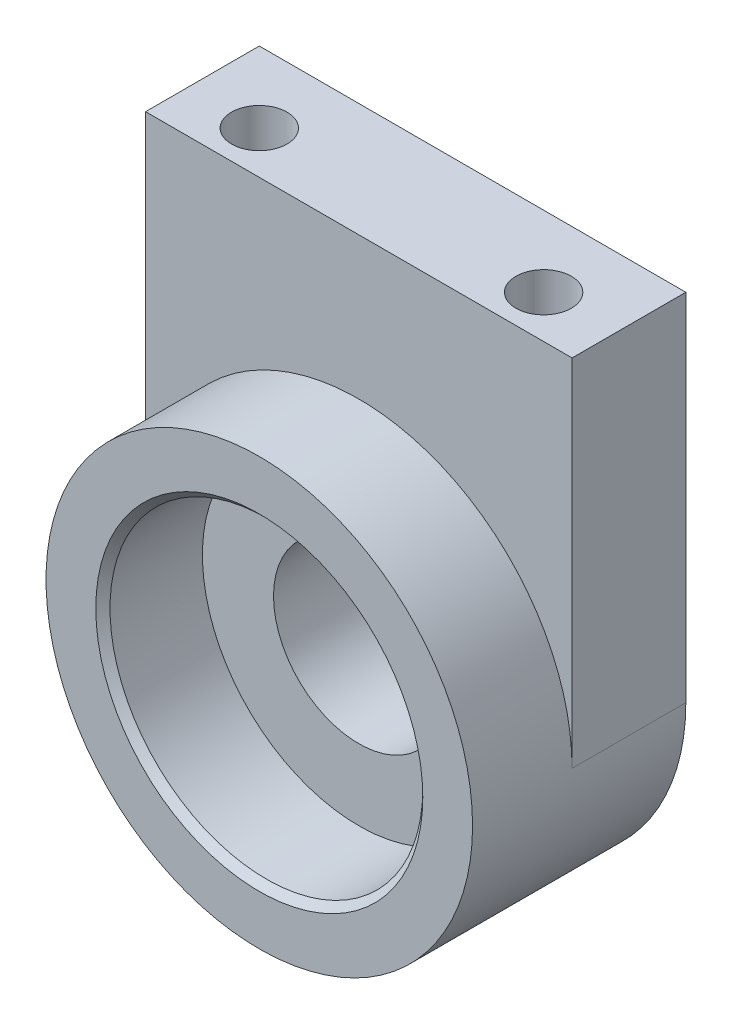
SolidWorks part; units mm, degrees
ref_plane "Front Plane" through (0, 0, 0) normal (0, 0, 1) x (1, 0, 0)
ref_plane "Top Plane" through (0, 0, 0) normal (0, 1, 0) x (1, 0, 0)
ref_plane "Right Plane" through (0, 0, 0) normal (1, 0, 0) x (0, 0, -1)
sketch "Sketch1" plane through (0, 0, 0) normal (0, 0, 1) x (1, 0, 0)
  circle A0 centre (0, 0) radius 11
  circle A1 centre (0, 0) radius 15
  dimension "D1" = 22
  dimension "D2" = 30
extrude "Boss-Extrude1" add sketch "Sketch1" along normal blind 7
sketch "Sketch3" plane through (0, 0, 0) normal (0, 0, -1) x (-1, 0, 0)
  line L0 (-15, 0) -> (-15, 25)
  line L1 (-15, 25) -> (15, 25)
  line L2 (15, 25) -> (15, 0)
  circle A1 centre (0, 0) radius 15
  arc A2 (-15, 0) -> (15, 0) centre (0, 0) ccw
  dimension "D2" = 25
  dimension "D1" = 0
extrude "Boss-Extrude2" add sketch "Sketch3" along normal blind 8
sketch "Sketch4" plane through (0, 25, 0) normal (0, 1, 0) x (1, 0, 0)
  line L0 (-12.5, 3) -> (12.5, 3) construction
  line L1 (-15, 8) -> (-15, 0) construction
  line L2 (15, 8) -> (15, 0) construction
  line L3 (-15, 0) -> (15, 0) construction
  circle A0 centre (-10, 3) radius 1.95
  circle A1 centre (10, 3) radius 1.95
  dimension "D1" = 3.9
  dimension "D2" = 3.9
  dimension "D3" = 5
  dimension "D4" = 5
  dimension "D5" = 3
extrude "Cut-Extrude1" cut sketch "Sketch4" against normal blind 6
fillet "Fillet1" [suppressed] radius 5
sketch "Sketch5" plane through (0, 0, 0) normal (0, 0, 1) x (1, 0, 0)
  circle A0 centre (0, 0) radius 6
  dimension "D1" = 12
extrude "Cut-Extrude2" cut sketch "Sketch5" against normal up to surface (8 mm away) up to face at (0, 8.75, -8)
chamfer "Chamfer1" distance 0.5 angle 45 1 edges at (11, 0, 7)
